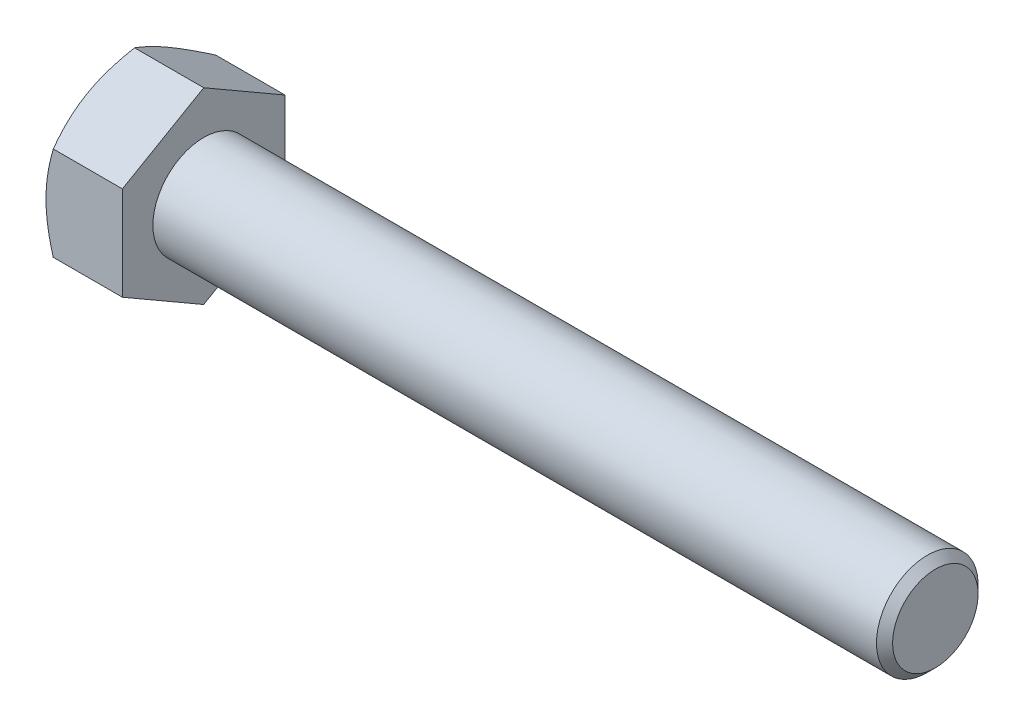
SolidWorks part; units mm, degrees
ref_plane "Plane1" through (0, 0, 0) normal (0, 0, 1) x (1, 0, 0)
ref_plane "Plane2" through (0, 0, 0) normal (0, 1, 0) x (1, 0, 0)
ref_plane "Plane3" through (0, 0, 0) normal (1, 0, 0) x (0, 0, -1)
sketch "Sketch1" plane through (0, 0, 0) normal (1, 0, 0) x (0, 0, -1)
  line L0 (6.35, 3.6662) -> (6.35, -3.6662)
  line L1 (-6.35, 3.6662) -> (-6.35, -3.6662)
  line L2 (6.35, -3.6662) -> (0, -7.3323)
  line L3 (0, -7.3323) -> (-6.35, -3.6662)
  line L4 (6.35, 3.6662) -> (0, 7.3323)
  line L5 (0, 7.3323) -> (-6.35, 3.6662)
  dimension "Width_flats" = 12.7
  dimension "D2" = 120
  dimension "D3" = 6.35
  dimension "D4" = 6.35
  dimension "D5" = 6.35
extrude "BaseHead" add sketch "Sketch1" along normal blind 5.969
sketch "BodySke" plane through (0, 0, 0) normal (0, 0, 1) x (1, 0, 0)
  line L0 (0, 3.6662) -> (0, -3.6662) construction
  line L1 (0, 0) -> (63.119, 0)
  line L2 (0, 0) -> (0, 3.9688)
  line L3 (0, 3.9688) -> (62.4891, 3.9688)
  line L4 (63.119, 0) -> (63.119, 3.3388)
  line L5 (5.969, 7.3323) -> (5.969, 3.6662) construction
  line L6 (63.119, 3.3388) -> (62.4891, 3.9688)
  line L7 (0, 0) -> (96.52, 0) construction
  line L8 (63.119, -3.3388) -> (62.4891, -3.9688) construction
  line L9 (0, -3.9688) -> (62.4891, -3.9688) construction
  line L10 (7.0282, 15.24) -> (7.0282, -2.54) construction
  line L11 (40.894, 15.24) -> (40.894, -2.54) construction
  line L12 (5.969, 3.6662) -> (5.969, -3.6662) construction
  dimension "Length" = 57.15
  dimension "Body_ch_ang" = 45
  dimension "Diameter" = 7.9375
  dimension "Minor_dia" = 6.6777
  dimension "Advance" = 1.0592
  dimension "Thread_nom" = 22.225
revolve "BaseBody" add sketch "BodySke" angle 360 about L7
cosmetic thread "ThreadCosmetic" [suppressed] parameters "Thread_length"=22.225, "Thread_minor"=6.6777
sketch "Sketch3" plane through (0, 0, 0) normal (0, 0, 1) x (1, 0, 0)
  line L0 (0, 6.35) -> (4.2333, 13.6823)
  line L1 (0, 7.3323) -> (0, 3.6662) construction
  line L2 (4.2333, 13.6823) -> (4.2333, 20.0323)
  line L3 (4.2333, 20.0323) -> (-12.7, 20.0323)
  line L4 (-12.7, 20.0323) -> (-12.7, 6.35)
  line L5 (-12.7, 6.35) -> (0, 6.35)
  line L6 (0, 0) -> (99.06, 0) construction
  line L7 (5.969, 7.3323) -> (0, 7.3323) construction
  dimension "D1" = 6.35
  dimension "D2" = 6.35
  dimension "D3" = 12.7
  dimension "D4" = 6.35
  dimension "Head_ch_ang" = 30
revolve "HeadChamfer" cut sketch "Sketch3" angle 360 about L6
fillet "HeadFillet" [suppressed] radius 0.762
sketch "ThdSchSke" plane through (0, 0, 0) normal (0, 0, 1) x (1, 0, 0)
  line L0 (40.894, -3.3388) -> (40.4529, -3.9688)
  line L1 (40.894, -3.3388) -> (41.3351, -3.9688)
  line L2 (41.3351, -3.9688) -> (41.3351, -4.9609)
  line L3 (-3.175, 0) -> (5.1513, 0) construction
  line L5 (41.3351, -4.9609) -> (40.4529, -4.9609)
  line L6 (40.4529, -4.9609) -> (40.4529, -3.9688)
  dimension "Thread_minor" = 6.6777
  dimension "Diameter" = 7.9375
  dimension "Start" = 40.894
  dimension "SideAngle" = 55
  dimension "VeeAngle" = 70
  dimension "Overcut" = 9.9219
revolve "ThreadSchematic" [suppressed] cut sketch "ThdSchSke" angle 360 about L3
pattern_linear "ThdSchPat" [suppressed]
equation "\"D3@Sketch1\" = \"Width_flats@Sketch1\" / 2"
equation "\"D4@Sketch1\" = \"D3@Sketch1\""
equation "\"D5@Sketch1\" = \"D4@Sketch1\""
equation "\"Thread_minor@ThreadCosmetic\" = \"Minor_dia@BodySke\""
equation "\"D1@Sketch3\" = \"Width_flats@Sketch1\" / 2"
equation "\"Thread_length@ThreadCosmetic\" = ((sgn( (\"Length@BodySke\" - \"Advance@BodySke\" ) - \"Thread_nom@BodySke\" )-1)*( (\"Length@BodySke\" - \"Advance@BodySke\" ) - \"Thread_nom@BodySke\" ))/-2+ \"Thread_nom@BodySke\""
equation "\"Thread_minor@ThdSchSke\" = \"Minor_dia@BodySke\""
equation "\"Diameter@ThdSchSke\" = \"Diameter@BodySke\""
equation "\"Overcut@ThdSchSke\" = \"Diameter@BodySke\" * 1.25"
equation "\"Start@ThdSchSke\" = \"Head_ht@BaseHead\" + \"Length@BodySke\" - \"Thread_length@ThreadCosmetic\"  '---Non-countersunk---"
equation "\"Num_threads@ThdSchPat\" = int( \"Thread_length@ThreadCosmetic\" / \"Advance@BodySke\" + 0.999 )  + 1"
equation "\"Advance@ThdSchPat\" = \"Thread_length@ThreadCosmetic\" /  (\"Num_threads@ThdSchPat\" - 1) 'relax it"
equation "\"Num_threads@ThdSchPat\" = \"Num_threads@ThdSchPat\" - sgn( \"Num_threads@ThdSchPat\" - 1) '---chamfered tips only---"
